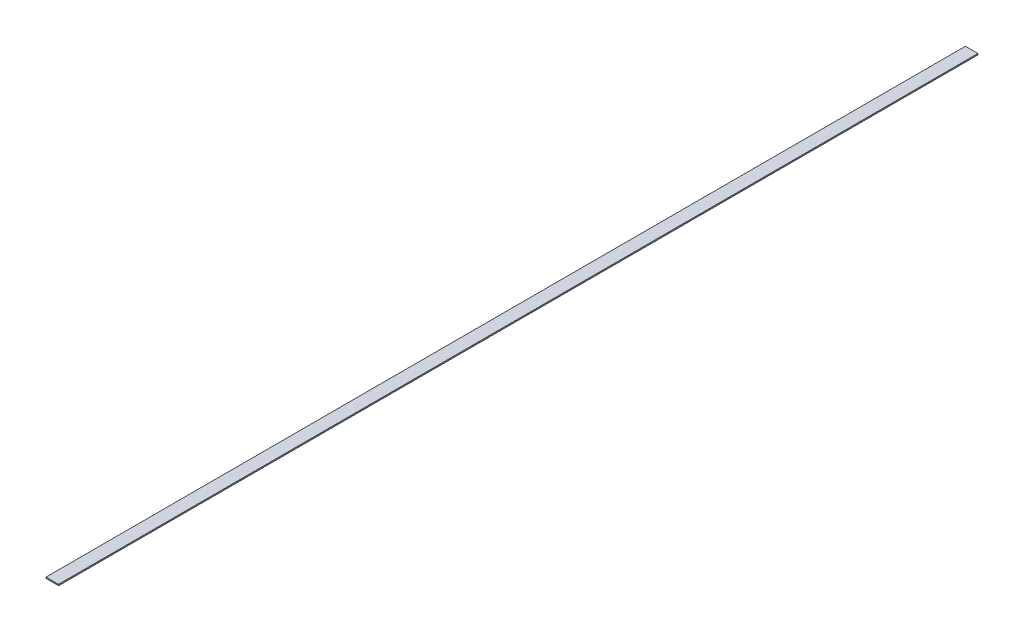
SolidWorks part; units mm, degrees
ref_plane "Front Plane" through (0, 0, 0) normal (0, 0, 1) x (1, 0, 0)
ref_plane "Top Plane" through (0, 0, 0) normal (0, 1, 0) x (1, 0, 0)
ref_plane "Right Plane" through (0, 0, 0) normal (1, 0, 0) x (0, 0, -1)
sketch "Sketch1" plane through (0, 0, 0) normal (0, 1, 0) x (1, 0, 0)
  line L0 (0, 0) -> (0, 3721.1)
  line L1 (0, 3721.1) -> (-50.8, 3721.1)
  line L2 (-50.8, 3721.1) -> (-50.8, 0)
  line L3 (-50.8, 0) -> (0, 0)
  dimension "D1" = 50.8
  dimension "D2" = 3721.1
extrude "Boss-Extrude1" add sketch "Sketch1" along normal blind 5.08
